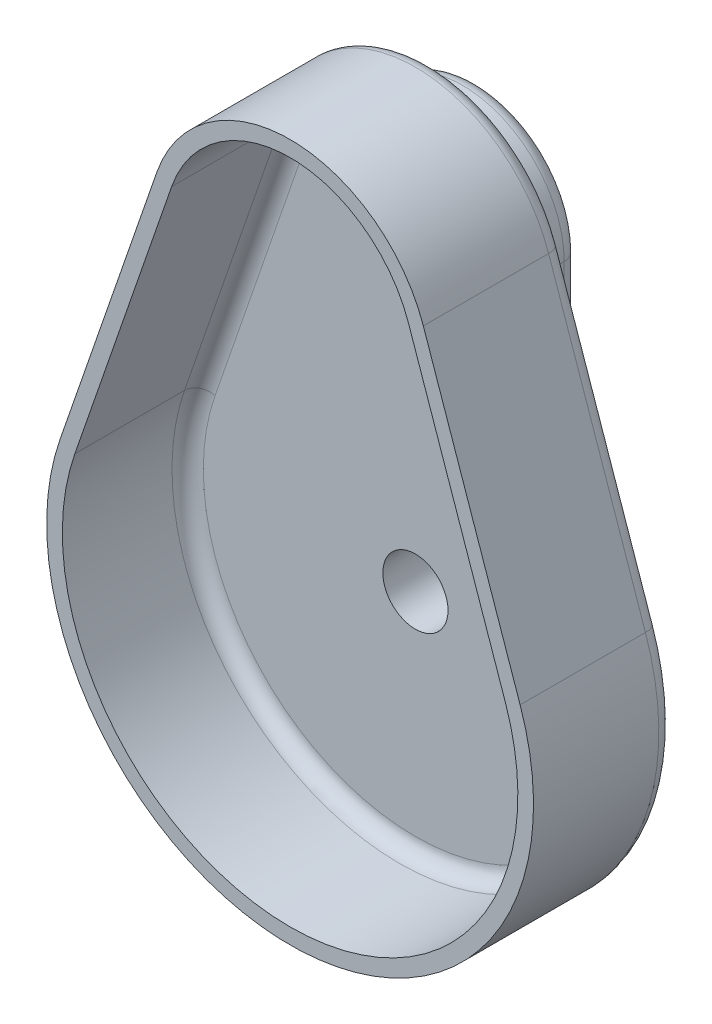
SolidWorks part; units mm, degrees
ref_plane "Front Plane" through (0, 0, 0) normal (0, 0, 1) x (1, 0, 0)
ref_plane "Top Plane" through (0, 0, 0) normal (0, 1, 0) x (1, 0, 0)
ref_plane "Right Plane" through (0, 0, 0) normal (1, 0, 0) x (0, 0, -1)
sketch "Sketch1" plane through (0, 0, 0) normal (0, 0, 1) x (1, 0, 0)
  line L0 (0, 31.75) -> (0, 0) construction
  line L1 (10.3187, 31.75) -> (10.3187, 0)
  line L2 (-10.3187, 31.75) -> (-10.3187, 0)
  circle A0 centre (0, 0) radius 3.302
  circle A1 centre (0, 31.75) radius 3.302
  arc A2 (10.3187, 31.75) -> (-10.3187, 31.75) centre (0, 31.75) ccw
  arc A3 (-10.3187, 0) -> (10.3187, 0) centre (0, 0) ccw
  point P5 (0, 15.875)
  dimension "D1" = 6.604
  dimension "D2" = 6.604
  dimension "D4" = 10.3187
  dimension "D3" = 31.75
extrude "Boss-Extrude1" add sketch "Sketch1" along normal blind 6.35
sketch "Sketch2" plane through (0, 0, 0) normal (0, 0, -1) x (-1, 0, 0)
  line L0 (-23.3135, 8.067) -> (-13.502, 36.422)
  line L1 (23.3135, 8.067) -> (13.502, 36.422)
  arc A0 (13.502, 36.422) -> (-13.502, 36.422) centre (0, 31.75) ccw
  arc A1 (-23.3135, 8.067) -> (23.3135, 8.067) centre (0, 0) ccw
  circle A3 centre (0, 0) radius 3.302
  circle A4 centre (0, 0) radius 3.302
  circle A5 centre (0, 31.75) radius 3.302
  circle A6 centre (0, 31.75) radius 3.302
  circle A7 centre (0, 0) radius 22.225 construction
  circle A8 centre (0, 31.75) radius 11.1125 construction
  dimension "D1" = 49.3395
  dimension "D2" = 28.575
  dimension "D5" = 44.45
  dimension "D6" = 22.225
  dimension "D3" = 0
  dimension "D4" = 0
extrude "Boss-Extrude2" add sketch "Sketch2" along normal blind 1.5875 from surface at -6.35 starting at face at (3.302, 0, 6.35)
sketch "Sketch3" plane through (0, 0, 6.35) normal (0, 0, 1) x (1, 0, 0)
  line L0 (21.8133, 7.5479) -> (12.0018, 35.9029)
  line L1 (-12.0018, 35.9029) -> (-21.8133, 7.5479)
  line L2 (-13.502, 36.422) -> (-23.3135, 8.067)
  line L3 (23.3135, 8.067) -> (13.502, 36.422)
  line L4 (-13.502, 36.422) -> (-23.3135, 8.067)
  line L5 (23.3135, 8.067) -> (13.502, 36.422)
  arc A0 (-21.8133, 7.5479) -> (21.8133, 7.5479) centre (0, 0) ccw
  arc A1 (12.0018, 35.9029) -> (-12.0018, 35.9029) centre (0, 31.75) ccw
  arc A2 (13.502, 36.422) -> (-13.502, 36.422) centre (0, 31.75) ccw
  arc A3 (-23.3135, 8.067) -> (23.3135, 8.067) centre (0, 0) ccw
  arc A4 (13.502, 36.422) -> (-13.502, 36.422) centre (0, 31.75) ccw
  arc A5 (-23.3135, 8.067) -> (23.3135, 8.067) centre (0, 0) ccw
  dimension "D1" = 0
  dimension "D2" = 1.5875
extrude "Boss-Extrude3" add sketch "Sketch3" along normal blind 12.7
fillet "Fillet1" radius 1.5875 12 edges at (-16.9075, 21.7254, 6.35) (0, 44.45, 6.35) (16.9075, 21.7254, 6.35) (-18.4078, 22.2445, 4.7625) (0, 46.0375, 4.7625) (18.4078, 22.2445, 4.7625) (0, -10.3187, 4.7625) (-10.3187, 15.875, 4.7625) (0, 42.0687, 4.7625) (0, -23.0822, 6.35) (0, -24.6697, 4.7625) (10.3187, 15.875, 4.7625)
fillet "Fillet2" radius 1.5875 4 edges at (-10.3187, 15.875, 0) (0, 42.0687, 0) (10.3187, 15.875, 0) (0, -10.3187, 0)
